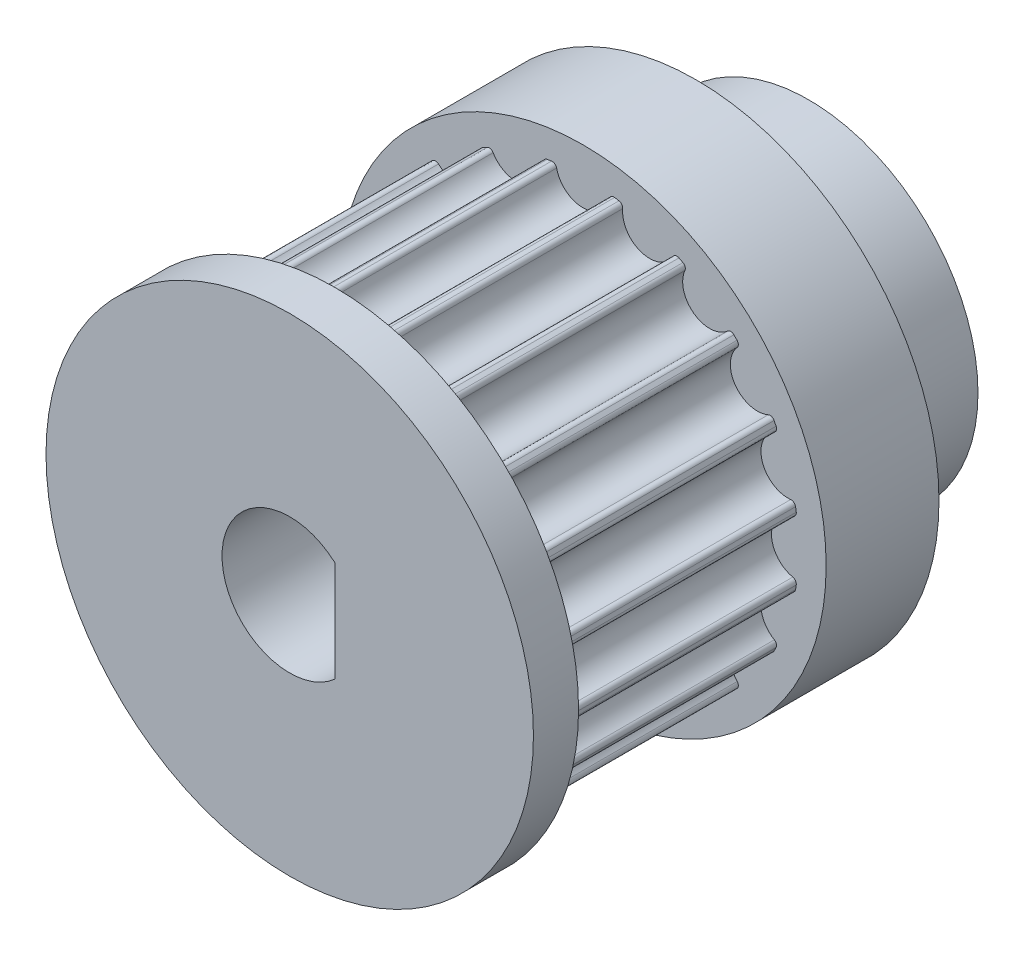
SolidWorks part; units mm, degrees
ref_plane "Front Plane" through (0, 0, 0) normal (0, 0, 1) x (1, 0, 0)
ref_plane "Top Plane" through (0, 0, 0) normal (0, 1, 0) x (1, 0, 0)
ref_plane "Right Plane" through (0, 0, 0) normal (1, 0, 0) x (0, 0, -1)
sketch "Sketch1" plane through (0, 0, 0) normal (0, 0, 1) x (1, 0, 0)
  line L0 (0, 0) -> (0, 9.5495) construction
  circle A0 centre (0, 0) radius 9.5495
  circle A1 centre (0, 9.5495) radius 1.2
  circle A2 centre (2.951, 9.0821) radius 1.2
  circle A3 centre (5.6131, 7.7257) radius 1.2
  circle A4 centre (7.7257, 5.6131) radius 1.2
  circle A5 centre (9.0821, 2.951) radius 1.2
  circle A6 centre (9.5495, 0) radius 1.2
  circle A7 centre (9.0821, -2.951) radius 1.2
  circle A8 centre (7.7257, -5.6131) radius 1.2
  circle A9 centre (5.6131, -7.7257) radius 1.2
  circle A10 centre (2.951, -9.0821) radius 1.2
  circle A11 centre (0, -9.5495) radius 1.2
  circle A12 centre (-2.951, -9.0821) radius 1.2
  circle A13 centre (-5.6131, -7.7257) radius 1.2
  circle A14 centre (-7.7257, -5.6131) radius 1.2
  circle A15 centre (-9.0821, -2.951) radius 1.2
  circle A16 centre (-9.5495, 0) radius 1.2
  circle A17 centre (-9.0821, 2.951) radius 1.2
  circle A18 centre (-7.7257, 5.6131) radius 1.2
  circle A19 centre (-5.6131, 7.7257) radius 1.2
  circle A20 centre (-2.951, 9.0821) radius 1.2
  dimension "D1" = 2.4
  dimension "D2" = 19.099
  dimension "D4" = 9.5495
  dimension "D3" = 20
extrude "Boss-Extrude1" add sketch "Sketch1" along normal blind 11
fillet "Fillet1" radius 0.2 41 edges at (1.1976, -9.4741, 5.5) (-1.1976, -9.4741, 5.5) (-1.7886, -9.3805, 5.5) (-4.0667, -8.6403, 5.5) (-4.5998, -8.3687, 5.5) (-6.5376, -6.9608, 5.5) (-6.9608, -6.5376, 5.5) (-8.3687, -4.5998, 5.5) (-8.6403, -4.0667, 5.5) (-9.3805, -1.7886, 5.5) (0, -8.3495, 0) (-9.4741, -1.1976, 5.5) (-9.4741, 1.1976, 5.5) (-9.3805, 1.7886, 5.5) (-8.6403, 4.0667, 5.5) (-8.3687, 4.5998, 5.5) (-6.9608, 6.5376, 5.5) (-6.5376, 6.9608, 5.5) (-4.5998, 8.3687, 5.5) (-4.0667, 8.6403, 5.5) (-1.7886, 9.3805, 5.5) (-1.1976, 9.4741, 5.5) (1.1976, 9.4741, 5.5) (4.0667, -8.6403, 5.5) (1.7886, -9.3805, 5.5) (6.5376, -6.9608, 5.5) (4.5998, -8.3687, 5.5) (8.3687, -4.5998, 5.5) (6.9608, -6.5376, 5.5) (9.3805, -1.7886, 5.5) (8.6403, -4.0667, 5.5) (9.4741, 1.1976, 5.5) (9.4741, -1.1976, 5.5) (8.6403, 4.0667, 5.5) (9.3805, 1.7886, 5.5) (6.9608, 6.5376, 5.5) (8.3687, 4.5998, 5.5) (4.5998, 8.3687, 5.5) (6.5376, 6.9608, 5.5) (1.7886, 9.3805, 5.5) (4.0667, 8.6403, 5.5)
sketch "Sketch2" plane through (0, 0, 11) normal (0, 0, 1) x (1, 0, 0)
  circle A0 centre (0, 0) radius 10.8
  dimension "D1" = 21.6
extrude "Boss-Extrude2" add sketch "Sketch2" along normal blind 2
sketch "Sketch3" plane through (0, 0, 0) normal (0, 0, -1) x (-1, 0, 0)
  circle A0 centre (0, 0) radius 10.7714
extrude "Boss-Extrude3" add sketch "Sketch3" along normal blind 10
ref_plane "Plane1" [suppressed] through (0, 0, 2) normal (0, 0, 1) x (1, 0, 0)
sketch "Sketch4" [suppressed] plane through (0, 0, 2) normal (0, 0, 1) x (1, 0, 0)
  circle A0 centre (0, 0) radius 8.3
  dimension "D1" = 16.6
extrude "Boss-Extrude5" [suppressed] add sketch "Sketch4" along normal blind 2
sketch "Sketch5" plane through (0, 0, 13) normal (0, 0, 1) x (1, 0, 0)
  line L1 (2, 2.2361) -> (4.1731, 2.2361)
  line L2 (2, 2.2361) -> (2, -2.2361)
  line L3 (2, -2.2361) -> (4.1731, -2.2361)
  line L4 (4.1731, 2.2361) -> (4.1731, -2.2361)
  circle A0 centre (0, 0) radius 3
  dimension "D1" = 6
  dimension "D2" = 2
extrude "Cut-Extrude1" cut sketch "Sketch5" against normal through all contours L2 A0
sketch "Sketch6" plane through (0, 0, -10) normal (0, 0, -1) x (-1, 0, 0)
  circle A0 centre (0, 0) radius 7.5
  dimension "D1" = 15
extrude "Cut-Extrude2" cut sketch "Sketch6" against normal blind 5 flip side to cut
